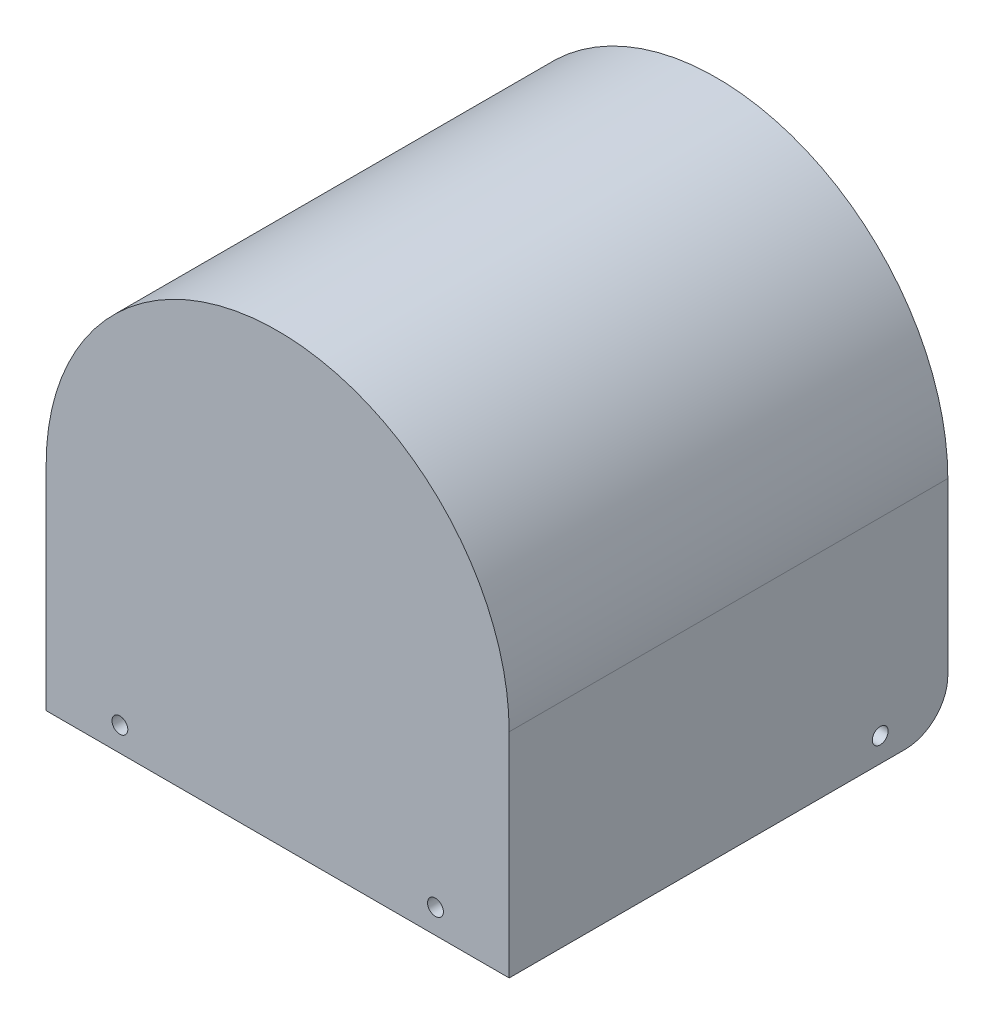
SolidWorks part; units mm, degrees
ref_plane "Front Plane" through (0, 0, 0) normal (0, 0, 1) x (1, 0, 0)
ref_plane "Top Plane" through (0, 0, 0) normal (0, 1, 0) x (1, 0, 0)
ref_plane "Right Plane" through (0, 0, 0) normal (1, 0, 0) x (0, 0, -1)
sketch "Sketch1" plane through (0, 0, 0) normal (0, 0, 1) x (1, 0, 0)
  line L0 (-36, 0) -> (-36, -35)
  line L1 (36, 0) -> (36, -35)
  line L2 (38, 0) -> (38, -35)
  line L3 (-38, 0) -> (-38, -35)
  line L4 (-38, -35) -> (-36, -35)
  line L5 (36, -35) -> (38, -35)
  arc A0 (-36, 0) -> (36, 0) centre (0, 0) cw
  arc A1 (-38, 0) -> (38, 0) centre (0, 0) cw
  dimension "D1" = 36
  dimension "D2" = 35
  dimension "D3" = 2
extrude "Boss-Extrude1" add sketch "Sketch1" along normal blind 72
sketch "Sketch2" plane through (0, 0, 0) normal (0, 1, 0) x (1, 0, 0)
  line L0 (-36, -72) -> (36, -72) construction
  line L1 (-36, -72) -> (36, -72)
  line L2 (-36, -72) -> (-36, -70)
  line L3 (-36, -70) -> (36, -70)
  line L4 (36, -72) -> (36, 0) construction
  line L5 (36, -70) -> (36, -72)
  dimension "D1" = 2
extrude "Boss-Extrude2" add sketch "Sketch2" against normal up to surface (35 mm away) and the other way up to surface up to face at (37, -35, 36) other way up to face at (0, 18, 36)
sketch "Sketch3" plane through (0, 0, 72) normal (0, 0, 1) x (1, 0, 0)
  line L0 (-38, -31) -> (38, -31) construction
  line L1 (-38, 0) -> (-38, -35) construction
  line L2 (38, -35) -> (38, 0) construction
  line L3 (-38, -35) -> (38, -35) construction
  line L4 (0, -31) -> (0, -35) construction
  circle A0 centre (-25.9, -31) radius 1.3
  circle A1 centre (25.9, -31) radius 1.3
  dimension "D3" = 2.6
  dimension "D1" = 4
  dimension "D2" = 51.8
extrude "Cut-Extrude1" cut sketch "Sketch3" against normal blind 10
sketch "Sketch4" plane through (38, 0, 0) normal (1, 0, 0) x (0, 0, -1)
  line L0 (-11.1, -35) -> (-11.1, 0) construction
  line L1 (-72, -35) -> (0, -35) construction
  line L2 (-72, 0) -> (0, 0) construction
  line L3 (0, -35) -> (0, 0) construction
  circle A0 centre (-11.1, -31) radius 1.3
  dimension "D2" = 2.6
  dimension "D1" = 11.1
  dimension "D3" = 4
extrude "Cut-Extrude2" cut sketch "Sketch4" against normal through all
fillet "Fillet1" radius 7 2 edges at (-37, -35, 0) (37, -35, 0)
